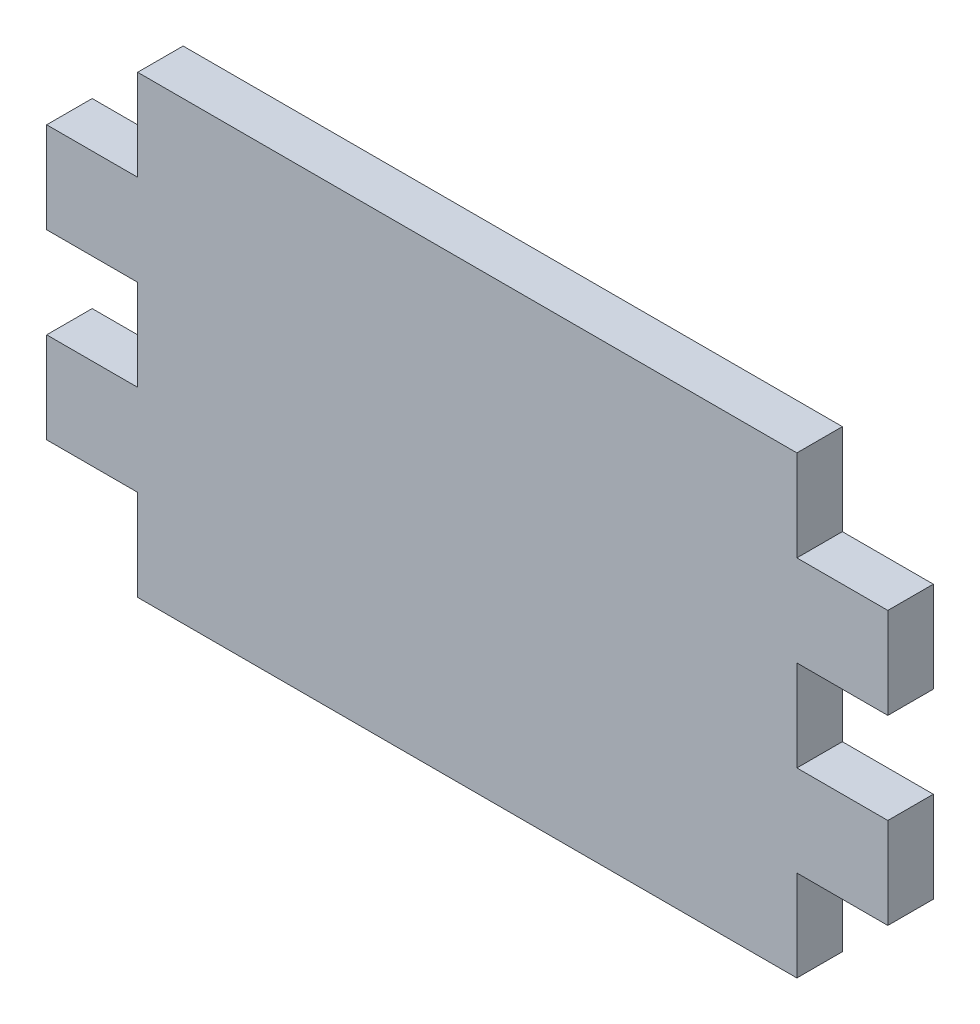
SolidWorks part; units mm, degrees
ref_plane "Front Plane" through (0, 0, 0) normal (0, 0, 1) x (1, 0, 0)
ref_plane "Top Plane" through (0, 0, 0) normal (0, 1, 0) x (1, 0, 0)
ref_plane "Right Plane" through (0, 0, 0) normal (1, 0, 0) x (0, 0, -1)
sketch "Sketch1" plane through (0, 0, 0) normal (0, 0, 1) x (1, 0, 0)
  line L0 (-23.0124, 31.75) -> (-23.0124, 0) construction
  line L1 (0, 0) -> (-46.0248, 0)
  line L2 (0, 0) -> (0, 6.35)
  line L3 (0, 31.75) -> (-46.0248, 31.75)
  line L4 (-46.0248, 0) -> (-46.0248, 6.35)
  line L5 (-52.3748, 19.05) -> (-46.0248, 19.05)
  line L6 (-52.3748, 12.7) -> (-46.0248, 12.7)
  line L7 (-46.0248, 25.4) -> (-46.0248, 31.75)
  line L8 (-52.3748, 6.35) -> (-46.0248, 6.35)
  line L9 (6.35, 6.35) -> (0, 6.35)
  line L10 (6.35, 12.7) -> (0, 12.7)
  line L11 (-52.3748, 25.4) -> (-46.0248, 25.4)
  line L12 (-46.0248, 12.7) -> (-46.0248, 19.05)
  line L13 (6.35, 19.05) -> (0, 19.05)
  line L14 (6.35, 25.4) -> (0, 25.4)
  line L15 (6.35, 25.4) -> (6.35, 19.05)
  line L16 (6.35, 12.7) -> (6.35, 6.35)
  line L19 (0, 12.7) -> (0, 19.05)
  line L20 (0, 25.4) -> (0, 31.75)
  line L21 (-46.0248, 25.4) -> (-46.0248, 6.35) construction
  line L22 (-52.3748, 12.7) -> (-52.3748, 6.35)
  line L23 (-52.3748, 25.4) -> (-52.3748, 19.05)
  dimension "D1" = 46.0248
  dimension "D2" = 31.75
  dimension "D5" = 6.35
  dimension "D6" = 2
extrude "Boss-Extrude1" add sketch "Sketch1" along normal blind 3.175
